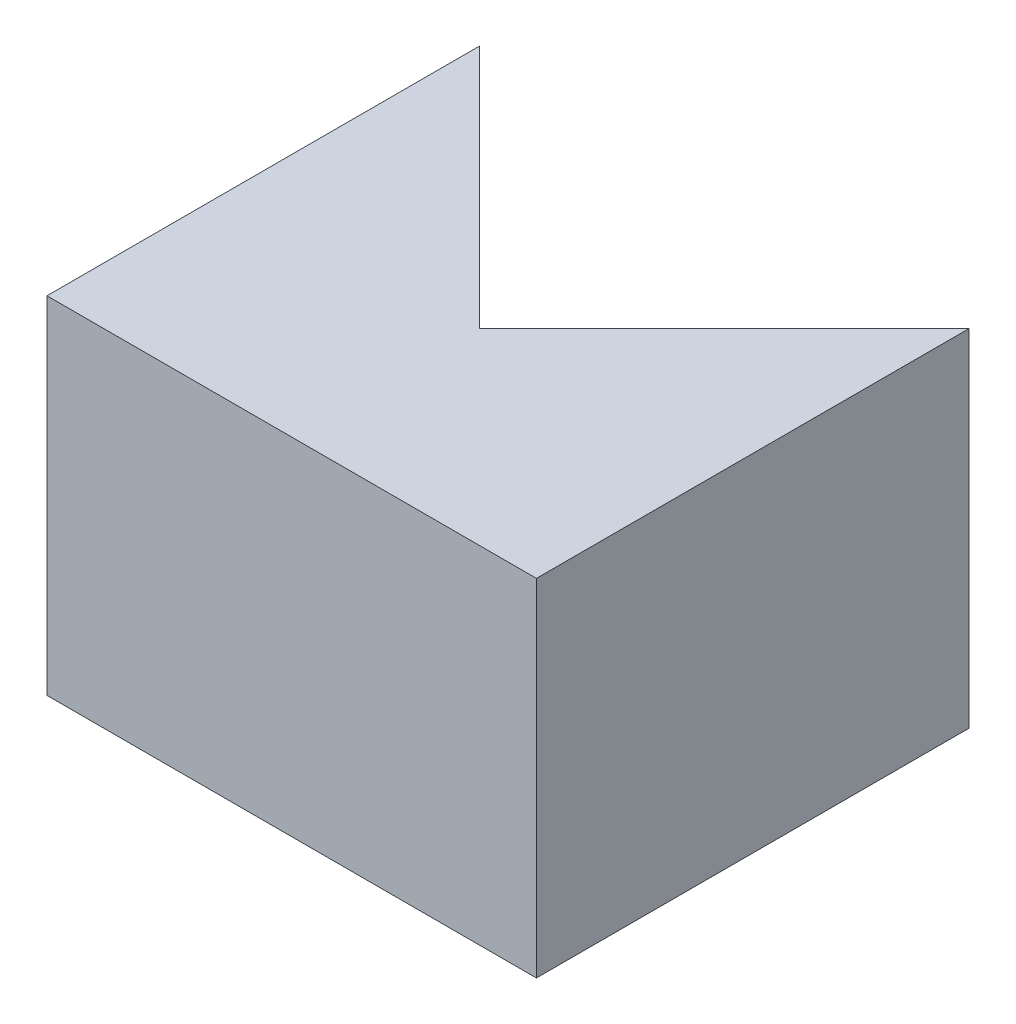
SolidWorks part; units mm, degrees
material "6061-T6 (SS)"
ref_plane "Front Plane" through (0, 0, 0) normal (0, 0, 1) x (1, 0, 0)
ref_plane "Top Plane" through (0, 0, 0) normal (0, 1, 0) x (1, 0, 0)
ref_plane "Right Plane" through (0, 0, 0) normal (1, 0, 0) x (0, 0, -1)
sketch "MotorProfile" plane through (0, 0, 0) normal (0, 1, 0) x (1, 0, 0)
  line L1 (-25.4, -25.4) -> (25.4, -25.4)
  line L2 (-25.4, -25.4) -> (-25.4, 25.4)
  line L3 (-25.4, 25.4) -> (25.4, 25.4)
  line L4 (25.4, -25.4) -> (25.4, 25.4)
  line L5 (-25.4, -25.4) -> (25.4, 25.4) construction
  line L6 (-25.4, 25.4) -> (25.4, -25.4) construction
  point P0 (0, 0)
  dimension "D1" = 50.8
sketch "Sketch2" plane through (0, 0, 0) normal (0, 1, 0) x (1, 0, 0)
  line L0 (-31.75, 25.4) -> (-31.75, -31.75)
  line L5 (-31.75, -31.75) -> (25.4, -31.75)
  line L6 (-25.4, -25.4) -> (-25.4, 25.4) construction
  line L7 (-31.75, 25.4) -> (-25.4, 25.4)
  line L8 (-25.4, 25.4) -> (-25.4, -25.4)
  line L9 (-25.4, -25.4) -> (25.4, -25.4)
  line L10 (25.4, -25.4) -> (25.4, -31.75)
  dimension "D1" = 57.15
  dimension "D2" = 6.35
sketch "Sketch3" plane through (0, 0, 0) normal (0, 1, 0) x (1, 0, 0)
  line L0 (17.9605, -17.9605) -> (-17.9605, 17.9605)
  line L1 (-17.9605, 17.9605) -> (-17.9605, -45.5395)
  line L2 (-17.9605, -45.5395) -> (53.8815, -45.5395)
  line L3 (17.9605, -17.9605) -> (53.8815, 17.9605)
  line L4 (53.8815, 17.9605) -> (53.8815, -45.5395)
  line L5 (0, 0) -> (104.1503, 0) construction
  point P4 (0, 0)
  dimension "D1" = 50.8
  dimension "D2" = 50.8
  dimension "D3" = 63.5
  dimension "D4" = 45
  dimension "D5" = 45
extrude "Boss-Extrude1" add sketch "Sketch3" along normal blind 50.8
extrude "Boss-Extrude2" [suppressed] add sketch "MotorProfile" along normal blind 25.4
extrude "Boss-Extrude3" [suppressed] add sketch "Sketch2" along normal blind 76.2
equation "\"1n\"=0.5"
